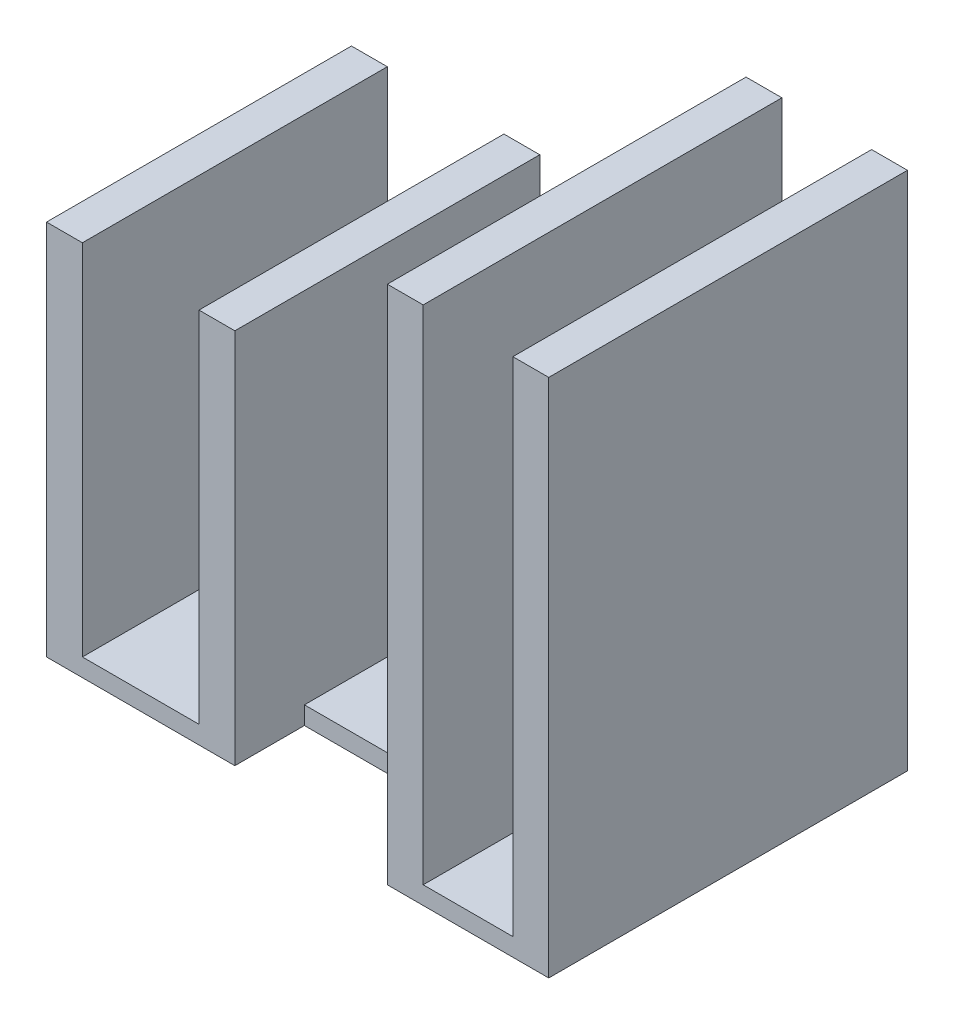
SolidWorks part; units mm, degrees
ref_plane "Front Plane" through (0, 0, 0) normal (0, 0, 1) x (1, 0, 0)
ref_plane "Top Plane" through (0, 0, 0) normal (0, 1, 0) x (1, 0, 0)
ref_plane "Right Plane" through (0, 0, 0) normal (1, 0, 0) x (0, 0, -1)
sketch "Sketch1" plane through (0, 0, 0) normal (0, 1, 0) x (1, 0, 0)
  line L0 (0, 0) -> (-6.5, 0) construction
  line L5 (-6.5, 0) -> (-6.5, 8.5) construction
  line L6 (-6.5, -8.5) -> (-8.5, -8.5)
  line L7 (-6.5, 8.5) -> (-8.5, 8.5)
  line L8 (-6.5, 8.5) -> (-6.5, -8.5)
  line L9 (-6.5, 0) -> (-8.5, 0)
  line L10 (-8.5, 8.5) -> (-8.5, -8.5)
  line L11 (-3.25, 0) -> (-3.25, 2.2043) construction
  line L12 (0, 8.5) -> (2, 8.5)
  line L13 (0, 8.5) -> (0, -8.5)
  line L14 (0, -8.5) -> (2, -8.5)
  line L15 (2, 8.5) -> (2, -8.5)
  line L16 (2, 0) -> (12, 0) construction
  line L19 (12, 10) -> (14, 10)
  line L21 (12, 0) -> (12, -10)
  line L22 (12, -10) -> (14, -10)
  line L23 (14, 10) -> (14, -10)
  line L24 (12, 0) -> (12, 10)
  line L25 (14, 0) -> (19, 0) construction
  line L26 (16.5, 0) -> (16.5, -2.6664) construction
  line L27 (21, -10) -> (19, -10)
  line L28 (21, 10) -> (19, 10)
  line L29 (19, 10) -> (19, -10)
  line L30 (21, 10) -> (21, -10)
  dimension "D1" = 6.5
  dimension "D2" = 8.5
  dimension "D3" = 2
  dimension "D4" = 10
  dimension "D5" = 10
  dimension "D6" = 2
  dimension "D7" = 5
extrude "Boss-Extrude1" add sketch "Sketch1" along normal blind 20 contours L7 L10 L9 L8 | L9 L10 L6 L8 | L30 L28 L29 L27 | L13 L14 L15 L12 | L23 L22 L21 L24 L19
sketch "Sketch2" plane through (0, 0, 0) normal (0, -1, 0) x (1, 0, 0)
  line L1 (21, 10) -> (12, 10)
  line L2 (21, 10) -> (21, -10)
  line L3 (21, -10) -> (12, -10)
  line L4 (12, 10) -> (12, -10)
  line L5 (2, -8.5) -> (-8.5, -8.5)
  line L6 (2, -8.5) -> (2, 8.5)
  line L7 (2, 8.5) -> (-8.5, 8.5)
  line L8 (-8.5, -8.5) -> (-8.5, 8.5)
  line L9 (2, 4.6221) -> (12, 4.6221)
  line L10 (2, 4.6221) -> (2, -3.5128)
  line L11 (2, -3.5128) -> (12, -3.5128)
  line L12 (12, 4.6221) -> (12, -3.5128)
extrude "Boss-Extrude2" add sketch "Sketch2" along normal blind 1 contours L6 L11 L4 L9 | L1 L4 L3 L2
sketch "Sketch3" plane through (0, 20, 0) normal (0, 1, 0) x (1, 0, 0)
  line L0 (14, 10) -> (14, -10) construction
  line L1 (12, 10) -> (14, 10)
  line L2 (12, 10) -> (12, -10)
  line L3 (12, -10) -> (14, -10)
  line L4 (14, 10) -> (14, -10)
  line L5 (19, -10) -> (14, -10) construction
  line L7 (19, -10) -> (21, -10)
  line L8 (19, -10) -> (19, 10)
  line L9 (19, 10) -> (21, 10)
  line L10 (21, -10) -> (21, 10)
extrude "Boss-Extrude3" add sketch "Sketch3" along normal blind 8
